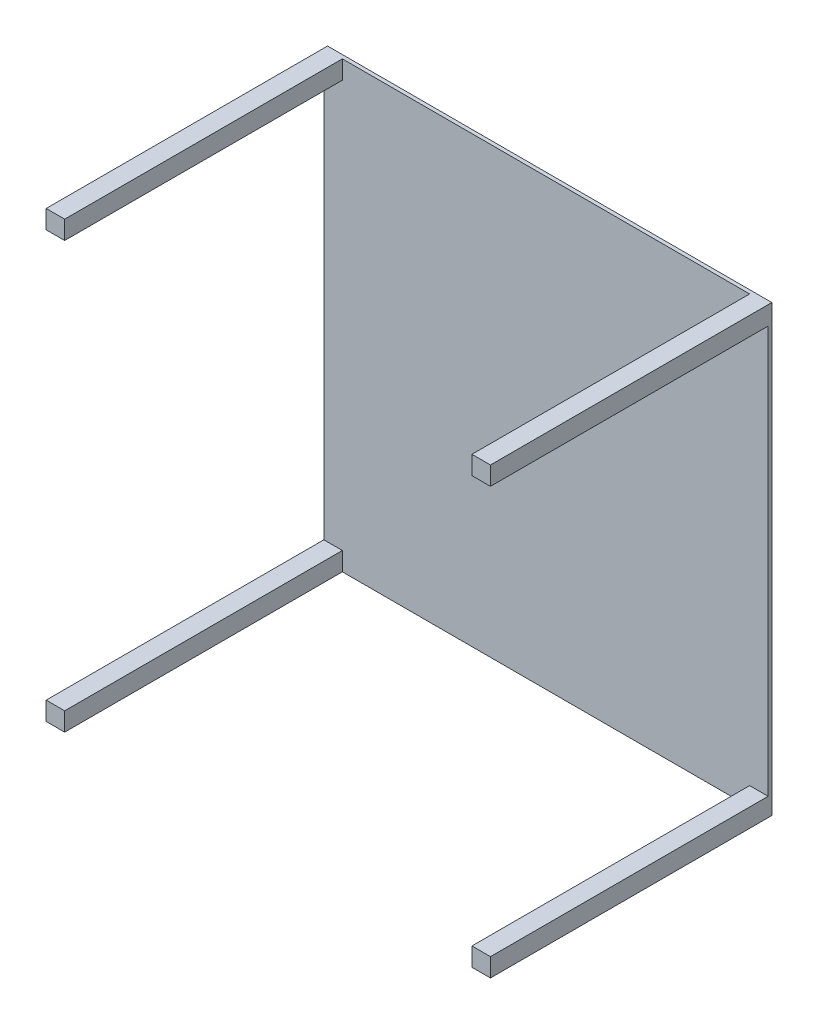
SolidWorks part; units mm, degrees
ref_plane "Front Plane" through (0, 0, 0) normal (0, 0, 1) x (1, 0, 0)
ref_plane "Top Plane" through (0, 0, 0) normal (0, 1, 0) x (1, 0, 0)
ref_plane "Right Plane" through (0, 0, 0) normal (1, 0, 0) x (0, 0, -1)
sketch "Sketch1" plane through (0, 0, 0) normal (0, 0, 1) x (1, 0, 0)
  line L1 (0, 0) -> (-1200, 0)
  line L2 (0, 0) -> (0, -1200)
  line L3 (0, -1200) -> (-1200, -1200)
  line L4 (-1200, 0) -> (-1200, -1200)
  dimension "D1" = 1200
  dimension "D2" = 1200
extrude "Boss-Extrude1" add sketch "Sketch1" along normal blind 10
sketch "Sketch2" plane through (0, 0, 10) normal (0, 0, 1) x (1, 0, 0)
  line L0 (-1200, -1150) -> (-1150, -1150)
  line L1 (-1200, 0) -> (-1150, 0)
  line L2 (-1200, 0) -> (-1200, -50)
  line L3 (-1200, -50) -> (-1150, -50)
  line L4 (-1150, 0) -> (-1150, -50)
  line L5 (-1200, -1150) -> (-1200, -1200)
  line L6 (-1200, -1200) -> (-1150, -1200)
  line L7 (-1150, -1150) -> (-1150, -1200)
  line L8 (-50, -1150) -> (0, -1150)
  line L9 (-50, -1150) -> (-50, -1200)
  line L10 (-50, -1200) -> (0, -1200)
  line L11 (0, -1150) -> (0, -1200)
  line L12 (-1200, -1200) -> (0, -1200) construction
  line L13 (-50, 0) -> (0, 0)
  line L14 (-50, 0) -> (-50, -50)
  line L15 (-50, -50) -> (0, -50)
  line L16 (0, 0) -> (0, -50)
  dimension "D1" = 50
  dimension "D2" = 50
  dimension "D3" = 50
  dimension "D4" = 50
  dimension "D5" = 50
  dimension "D6" = 50
  dimension "D7" = 50
  dimension "D8" = 50
extrude "Boss-Extrude2" add sketch "Sketch2" along normal blind 750
equation "\"R\"=50"
equation "\"D1@Sketch2\"=\"R\""
equation "\"D2@Sketch2\"=\"R\""
equation "\"D7@Sketch2\"=\"R\""
equation "\"D8@Sketch2\"=\"R\""
equation "\"D6@Sketch2\"=\"R\""
equation "\"D5@Sketch2\"=\"R\""
equation "\"D4@Sketch2\"=\"R\""
equation "\"D3@Sketch2\"=\"R\""
